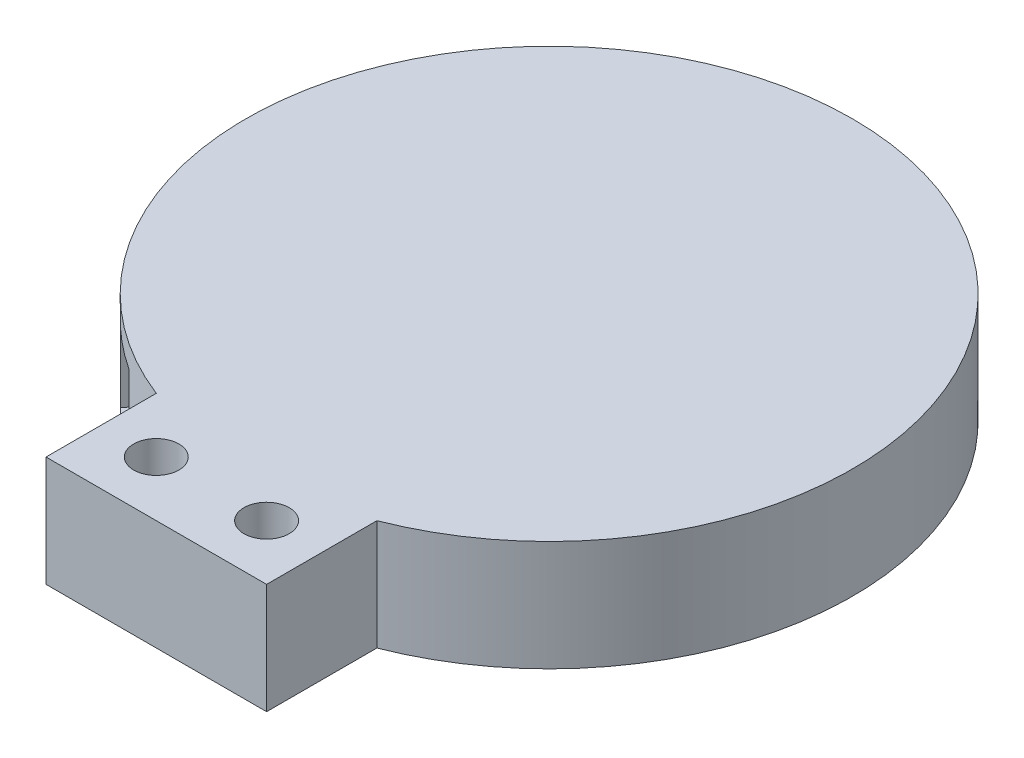
SolidWorks part; units mm, degrees
ref_plane "Спереди" through (0, 0, 0) normal (0, 0, 1) x (1, 0, 0)
ref_plane "Сверху" through (0, 0, 0) normal (0, 1, 0) x (1, 0, 0)
ref_plane "Справа" through (0, 0, 0) normal (1, 0, 0) x (0, 0, -1)
sketch "Sketch1" plane through (0, 0, 0) normal (0, 1, 0) x (1, 0, 0)
  circle A0 centre (0, 0) radius 55
  dimension "D1" = 110
extrude "Boss-Extrude1" add sketch "Sketch1" along normal blind 20
sketch "Sketch9" plane through (0, 0, 0) normal (0, -1, 0) x (1, 0, 0)
  line L0 (0, -55) -> (0, 55) construction
  line L2 (-20, 51.2348) -> (20, 51.2348)
  line L3 (-20, 51.2348) -> (-20, 71.2348)
  line L4 (-20, 71.2348) -> (20, 71.2348)
  line L5 (20, 51.2348) -> (20, 71.2348)
  line L6 (-20, 51.2348) -> (20, 71.2348) construction
  line L7 (-20, 71.2348) -> (20, 51.2348) construction
  circle A0 centre (0, 0) radius 55 construction
  point P5 (0, 61.2348)
  dimension "D1" = 40
  dimension "D2" = 20
extrude "Boss-Extrude4" add sketch "Sketch9" against normal up to surface (20 mm away) up to face at (0, 20, 55)
sketch "Sketch11" plane through (0, 20, 0) normal (0, 1, 0) x (1, 0, 0)
  line L0 (-20, -61.2348) -> (20, -61.2348) construction
  line L1 (-20, -71.2348) -> (-20, -51.2348) construction
  line L2 (20, -51.2348) -> (20, -71.2348) construction
  circle A0 centre (-10, -61.2348) radius 4.1
  circle A1 centre (10, -61.2348) radius 4.1
  point P10 (0, -61.2348)
  dimension "D1" = 8.2
  dimension "D2" = 20
  dimension "D3" = 10
extrude "Cut-Extrude6" cut sketch "Sketch11" against normal through all
sketch "Sketch12" plane through (0, 0, 0) normal (0, -1, 0) x (1, 0, 0)
  circle A0 centre (0, 0) radius 52
  arc A1 (-20, 51.2348) -> (20, 51.2348) centre (0, 0) ccw construction
  dimension "D1" = 3
extrude "Cut-Extrude7" cut sketch "Sketch12" against normal blind 17
sketch "Sketch13" plane through (0, 0, 0) normal (0, -1, 0) x (1, 0, 0)
  line L0 (-27.3295, 44.2391) -> (-38.8213, 34.5963)
  line L1 (-38.8213, 34.5963) -> (-36.2428, 41.3698)
  line L2 (-36.2428, 41.3698) -> (-27.3295, 44.2391)
  line L3 (0, 0) -> (-33.0754, 39.4177) construction
  line L4 (0, 0) -> (0, 52) construction
  circle A0 centre (0, 0) radius 52 construction
  arc A1 (-20, 51.2348) -> (20, 51.2348) centre (0, 0) ccw construction
  dimension "D1" = 15.0016
  dimension "D2" = 40
extrude "Boss-Extrude5" add sketch "Sketch13" against normal up to surface (17 mm away) up to face at (0, 17, -52)
sketch "Sketch14" plane through (-33.0754, 0, 39.4177) normal (0.6428, 0, -0.766) x (-0.766, 0, -0.6428)
  line L0 (7.5008, 8.5) -> (-7.5008, 8.5) construction
  line L1 (7.5008, 17) -> (7.5008, 0) construction
  line L2 (-7.5008, 17) -> (-7.5008, 0) construction
  line L4 (-6.4, 1) -> (6.4, 1)
  line L5 (-6.4, 1) -> (-6.4, 16)
  line L6 (-6.4, 16) -> (6.4, 16)
  line L7 (6.4, 1) -> (6.4, 16)
  line L8 (-6.4, 1) -> (6.4, 16) construction
  line L9 (-6.4, 16) -> (6.4, 1) construction
  point P6 (0, 8.5)
  dimension "D1" = 15
  dimension "D2" = 12.8
extrude "Cut-Extrude8" cut sketch "Sketch14" against normal through all
sketch "Sketch16" plane through (0, 0, 0) normal (0, -1, 0) x (1, 0, 0)
  line L0 (10, 61.2348) -> (-10, 61.2348) construction
  line L2 (-17.5, 68.7348) -> (17.5, 68.7348)
  line L3 (-17.5, 68.7348) -> (-17.5, 53.7348)
  line L4 (-17.5, 53.7348) -> (17.5, 53.7348)
  line L5 (17.5, 68.7348) -> (17.5, 53.7348)
  line L6 (-17.5, 68.7348) -> (17.5, 53.7348) construction
  line L7 (-17.5, 53.7348) -> (17.5, 68.7348) construction
  point P4 (0, 61.2348)
  dimension "D1" = 15
  dimension "D2" = 35
extrude "Cut-Extrude9" cut sketch "Sketch16" against normal blind 10
chamfer "Chamfer1" distance 1 angle 70 4 edges at (17.5, 0, 61.2348) (0, 0, 68.7348) (-17.5, 0, 61.2348) (0, 0, 53.7348)
